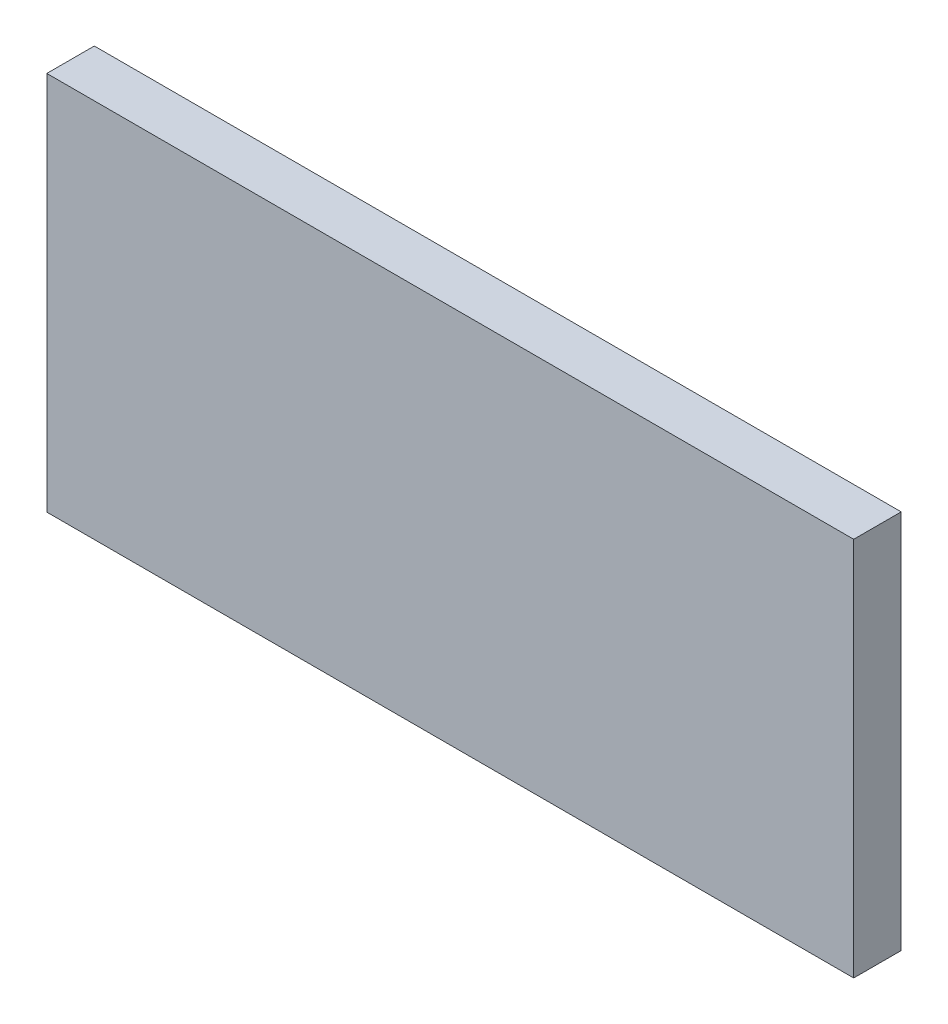
SolidWorks part; units mm, degrees
material "Acrílico (médio-alto impacto)"
ref_plane "Plano frontal" through (0, 0, 0) normal (0, 0, 1) x (1, 0, 0)
ref_plane "Plano superior" through (0, 0, 0) normal (0, 1, 0) x (1, 0, 0)
ref_plane "Plano direito" through (0, 0, 0) normal (1, 0, 0) x (0, 0, -1)
sketch "Esboço1" plane through (0, 0, 0) normal (0, 0, 1) x (1, 0, 0)
  line L1 (-42.1248, 13.2793) -> (42.8232, 13.2793)
  line L2 (-42.1248, 13.2793) -> (-42.1248, -26.7207)
  line L3 (-42.1248, -26.7207) -> (42.8232, -26.7207)
  line L4 (42.8232, 13.2793) -> (42.8232, -26.7207)
  dimension "D1" = 84.948
  dimension "D2" = 40
extrude "Ressalto-extrusão1" add sketch "Esboço1" along normal blind 5
